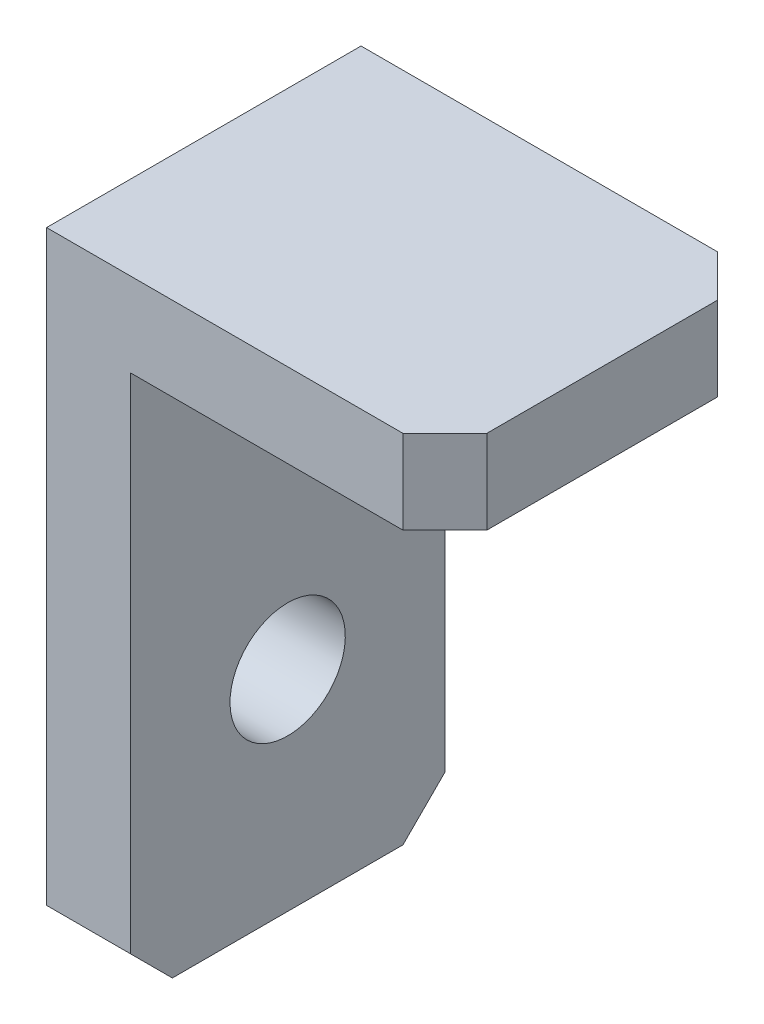
SolidWorks part; units mm, degrees
material "ABS"
ref_plane "Front Plane" through (0, 0, 0) normal (0, 0, 1) x (1, 0, 0)
ref_plane "Top Plane" through (0, 0, 0) normal (0, 1, 0) x (1, 0, 0)
ref_plane "Right Plane" through (0, 0, 0) normal (1, 0, 0) x (0, 0, -1)
sketch "Sketch1" plane through (0, 0, 0) normal (0, 0, 1) x (1, 0, 0)
  line L0 (0, 0) -> (19, 0)
  line L1 (19, 0) -> (19, -4)
  line L2 (19, -4) -> (4, -4)
  line L3 (4, -4) -> (4, -30)
  line L4 (4, -30) -> (0, -30)
  line L5 (0, -30) -> (0, 0)
  dimension "D1" = 15
  dimension "D2" = 4
  dimension "D3" = 30
  dimension "D4" = 4
extrude "Boss-Extrude1" add sketch "Sketch1" along normal blind 15
sketch "Sketch2" plane through (4, 0, 0) normal (1, 0, 0) x (0, 0, -1)
  line L0 (-7.5, -4) -> (-7.5, -30) construction
  line L1 (-15, -4) -> (0, -4) construction
  line L2 (-15, -30) -> (0, -30) construction
  line L3 (-15, 0) -> (0, 0) construction
  circle A0 centre (-7.5, -20) radius 2.75
  dimension "D1" = 5.5
  dimension "D2" = 20
extrude "Cut-Extrude1" cut sketch "Sketch2" against normal up to next
chamfer "Chamfer1" distance 2 angle 45 4 edges at (2, -30, 15) (2, -30, 0) (19, -2, 0) (19, -2, 15)
